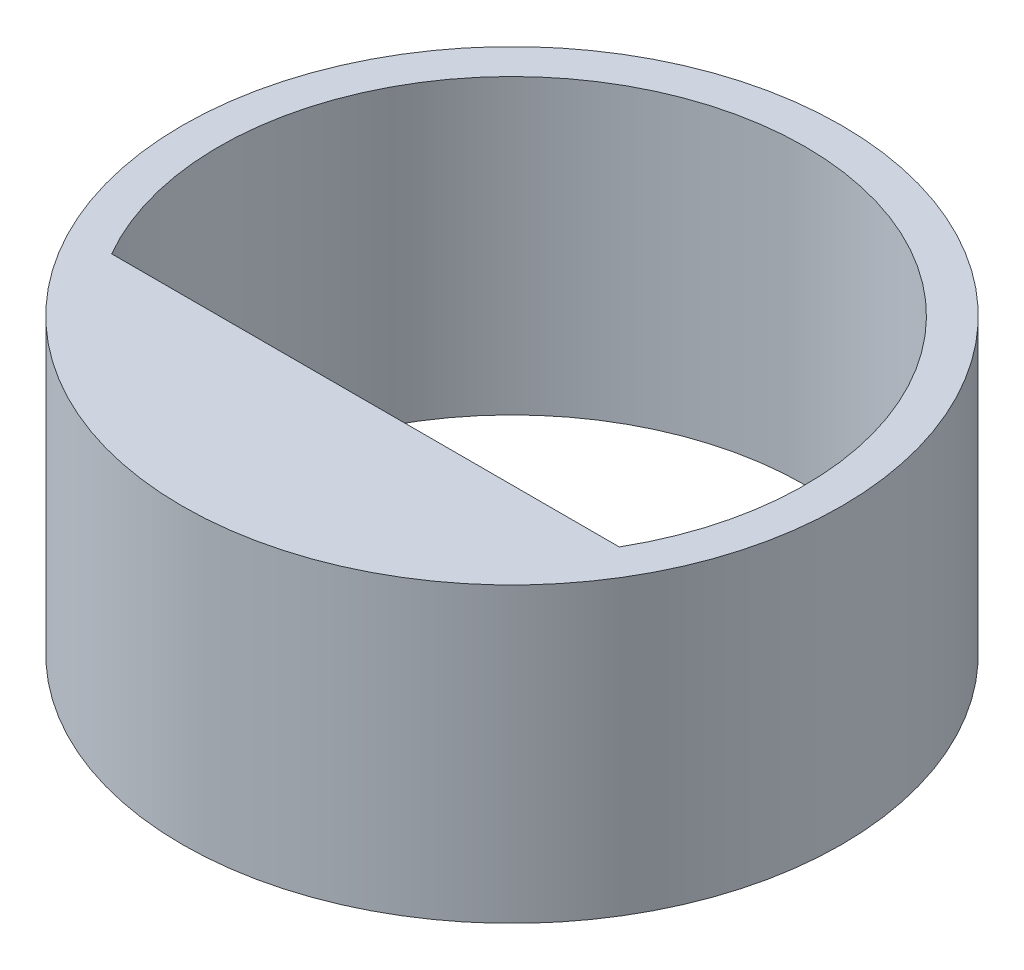
SolidWorks part; units mm, degrees
ref_plane "Front Plane" through (0, 0, 0) normal (0, 0, 1) x (1, 0, 0)
ref_plane "Top Plane" through (0, 0, 0) normal (0, 1, 0) x (1, 0, 0)
ref_plane "Right Plane" through (0, 0, 0) normal (1, 0, 0) x (0, 0, -1)
sketch "Sketch1" plane through (0, 0, 0) normal (0, 1, 0) x (1, 0, 0)
  line L0 (-1.7321, -1) -> (1.7321, -1)
  circle A0 centre (0, 0) radius 2.25
  circle A1 centre (0, 0) radius 2 construction
  arc A2 (-1.7321, -1) -> (1.7321, -1) centre (0, 0) cw
  dimension "D1" = 4.5
  dimension "D2" = 4
  dimension "D3" = 1
extrude "Boss-Extrude1" add sketch "Sketch1" along normal blind 2
